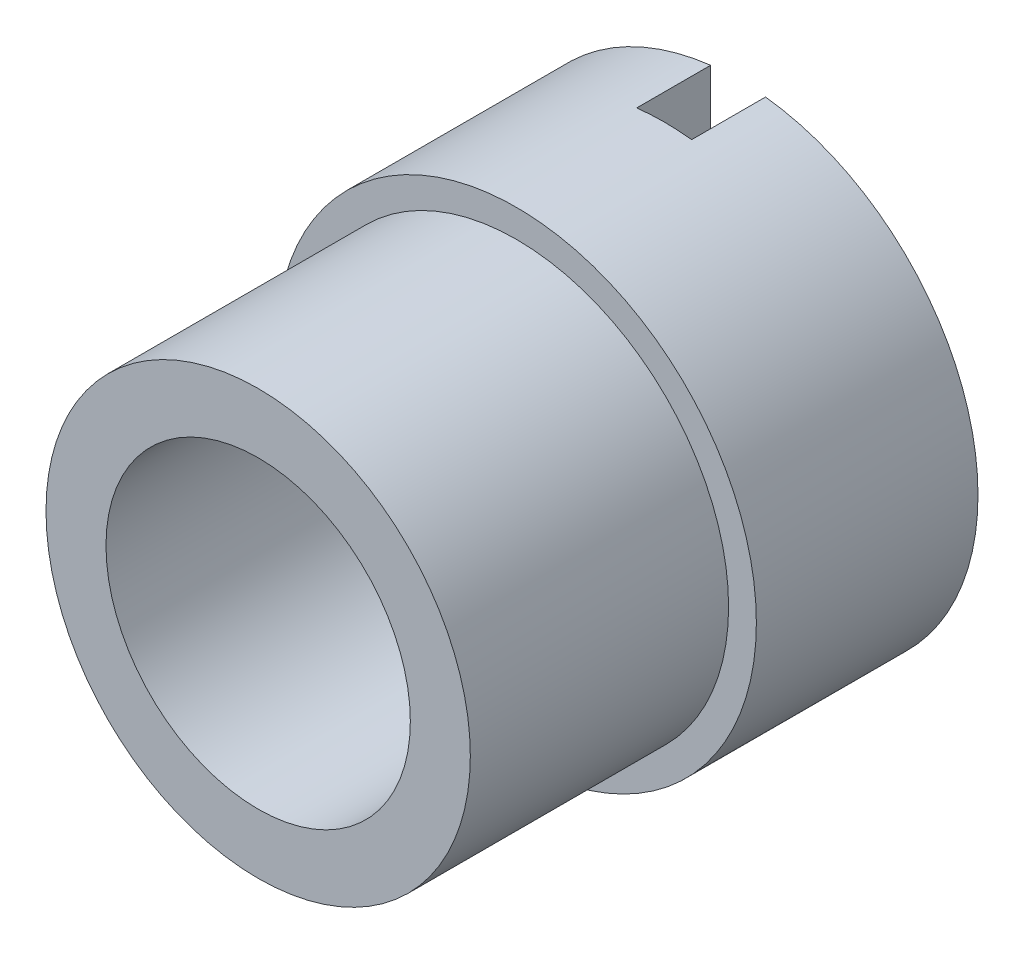
SolidWorks part; units mm, degrees
ref_plane "Front Plane" through (0, 0, 0) normal (0, 0, 1) x (1, 0, 0)
ref_plane "Top Plane" through (0, 0, 0) normal (0, 1, 0) x (1, 0, 0)
ref_plane "Right Plane" through (0, 0, 0) normal (1, 0, 0) x (0, 0, -1)
sketch "Sketch1" plane through (0, 0, 0) normal (0, 0, 1) x (1, 0, 0)
  circle A0 centre (0, 0) radius 6.5405
  circle A1 centre (0, 0) radius 10.3124
  dimension "D1" = 13.081
  dimension "D2" = 20.6248
extrude "Boss-Extrude1" add sketch "Sketch1" along normal mid plane 9.525
cosmetic thread "Cosmetic Thread1" parameters "D1"=9.525, "D2"=19.6248
cosmetic thread "Cosmetic Thread2" parameters "D1"=9.525, "D2"=19.6248
sketch "Sketch2" plane through (0, 0, 4.7625) normal (0, 0, 1) x (1, 0, 0)
  circle A0 centre (0, 0) radius 6.5405 construction
  circle A1 centre (0, 0) radius 6.5405
  circle A2 centre (0, 0) radius 9.1186
  dimension "D1" = 18.2372
extrude "Boss-Extrude2" add sketch "Sketch2" along normal blind 11.0998
sketch "Sketch3" plane through (0, 0, 0) normal (0, 1, 0) x (1, 0, 0)
  line L0 (6.5405, 4.7625) -> (-6.5405, 4.7625) construction
  line L1 (-1.1811, 1.5875) -> (1.1811, 1.5875)
  line L2 (-1.1811, 1.5875) -> (-1.1811, 4.7625)
  line L3 (-1.1811, 4.7625) -> (1.1811, 4.7625)
  line L4 (1.1811, 1.5875) -> (1.1811, 4.7625)
  line L5 (-1.1811, 1.5875) -> (1.1811, 4.7625) construction
  line L6 (-1.1811, 4.7625) -> (1.1811, 1.5875) construction
  point P0 (0, 3.175)
  point P7 (0, 0)
  dimension "D1" = 2.3622
  dimension "D2" = 3.175
extrude "Cut-Extrude1" cut sketch "Sketch3" against normal through all both and the other way through all
